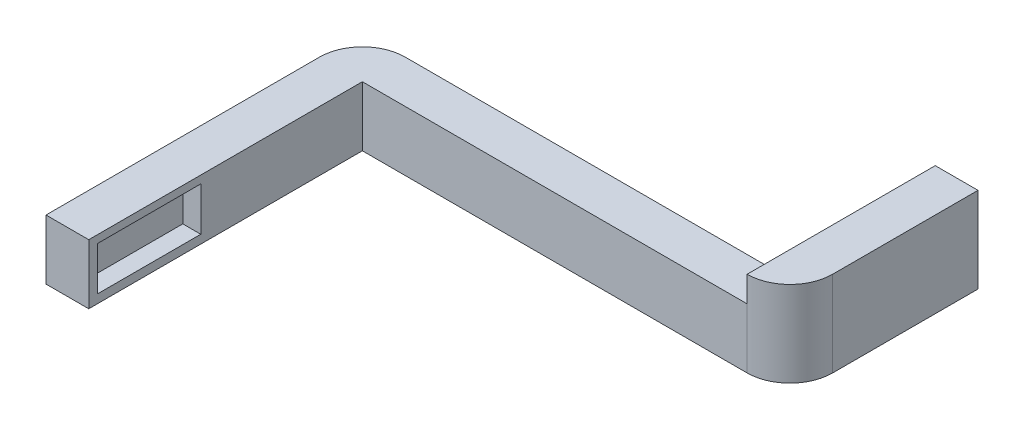
SolidWorks part; units mm, degrees
ref_plane "Front Plane" through (0, 0, 0) normal (0, 0, 1) x (1, 0, 0)
ref_plane "Top Plane" through (0, 0, 0) normal (0, 1, 0) x (1, 0, 0)
ref_plane "Right Plane" through (0, 0, 0) normal (1, 0, 0) x (0, 0, -1)
other "Configuration Table"
sketch "Sketch1" plane through (0, 0, 0) normal (0, 0, 1) x (1, 0, 0)
  line L1 (22.5, 3.5) -> (-22.5, 3.5)
  line L2 (22.5, 3.5) -> (22.5, -3.5)
  line L3 (22.5, -3.5) -> (-22.5, -3.5)
  line L4 (-22.5, 3.5) -> (-22.5, -3.5)
  line L5 (22.5, 3.5) -> (-22.5, -3.5) construction
  line L6 (22.5, -3.5) -> (-22.5, 3.5) construction
  point P0 (0, 0)
  dimension "D1" = 45
  dimension "D2" = 7
extrude "Boss-Extrude1" add sketch "Sketch1" along normal blind 5
sketch "Sketch2" plane through (-22.5, 0, 0) normal (-1, 0, 0) x (0, 0, 1)
  line L0 (5, -3.5) -> (0, -3.5) construction
  line L1 (5, 3.5) -> (-32, 3.5)
  line L2 (5, 3.5) -> (5, -3.5)
  line L3 (5, -3.5) -> (-32, -3.5)
  line L4 (-32, 3.5) -> (-32, -3.5)
  dimension "D1" = 37
extrude "Boss-Extrude2" add sketch "Sketch2" along normal blind 5
fillet "Fillet1" radius 5 1 edges at (-27.5, 0, 5)
sketch "Sketch3" plane through (22.5, 0, 0) normal (1, 0, 0) x (0, 0, -1)
  line L1 (0, 6.5) -> (-22, 6.5)
  line L2 (0, 6.5) -> (0, -3.5)
  line L3 (0, -3.5) -> (-22, -3.5)
  line L4 (-22, 6.5) -> (-22, -3.5)
  line L5 (-5, -3.5) -> (0, -3.5) construction
  line L6 (0, 13.6459) -> (0, -13.6459) construction
  dimension "D1" = 22
  dimension "D2" = 10
extrude "Boss-Extrude3" add sketch "Sketch3" along normal blind 5
fillet "Fillet2" radius 5 1 edges at (27.5, 1.5, 0)
sketch "Sketch4" plane through (-22.5, 0, 0) normal (1, 0, 0) x (0, 0, -1)
  line L1 (32, 3.5) -> (32, -3.5) construction
  line L3 (31, 2.6) -> (18.9, 2.6)
  line L4 (31, 2.6) -> (31, -2.5)
  line L5 (31, -2.5) -> (18.9, -2.5)
  line L6 (18.9, 2.6) -> (18.9, -2.5)
  line L7 (31, 2.6) -> (18.9, -2.5) construction
  line L8 (31, -2.5) -> (18.9, 2.6) construction
  line L9 (32, -3.5) -> (0, -3.5) construction
  point P0 (24.95, 0.05)
  dimension "D1" = 12.1
  dimension "D2" = 5.1
  dimension "D4" = 1
  dimension "D3" = 1
extrude "Cut-Extrude1" cut sketch "Sketch4" against normal blind 2.1
mirror "Mirror1" about plane through (-27.5, 3.5, -32) normal (0, 0, 1) of bodies 105
delete or keep bodies "Body-Delete/Keep 1" type keep bodies bodies 106
